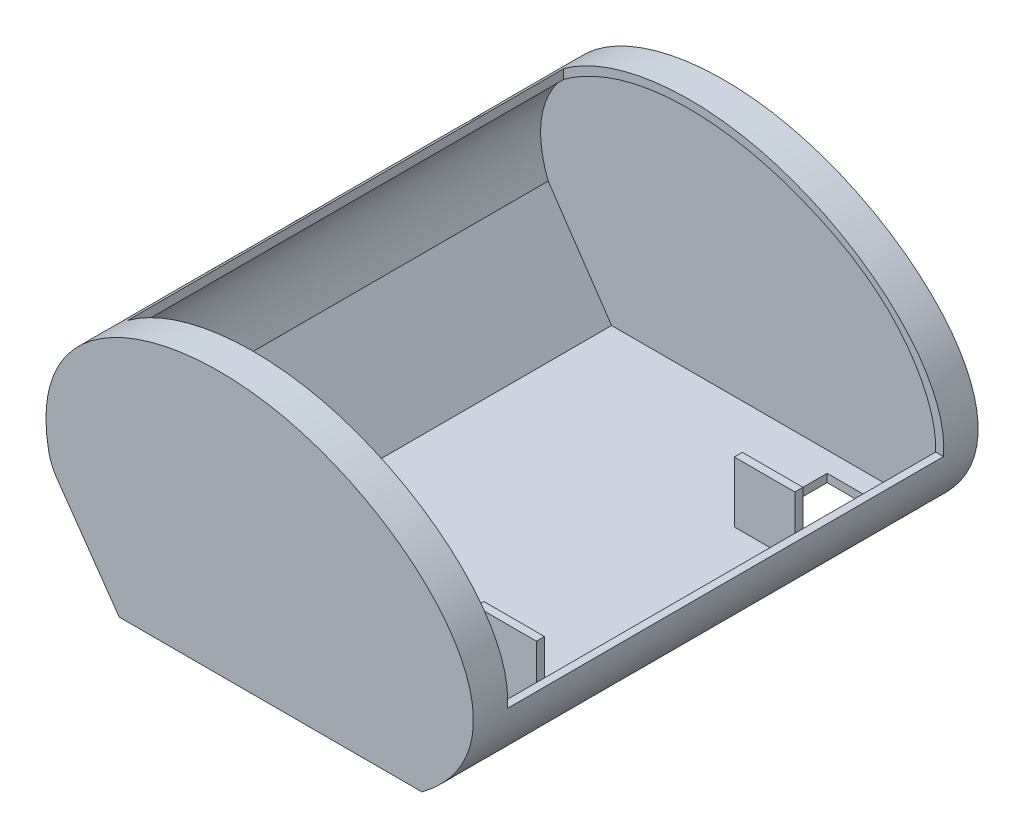
SolidWorks part; units mm, degrees
ref_plane "Front Plane" through (0, 0, 0) normal (0, 0, 1) x (1, 0, 0)
ref_plane "Top Plane" through (0, 0, 0) normal (0, 1, 0) x (1, 0, 0)
ref_plane "Right Plane" through (0, 0, 0) normal (1, 0, 0) x (0, 0, -1)
sketch "Sketch1" plane through (0, 0, 0) normal (0, 0, 1) x (1, 0, 0)
  line L0 (-74.4669, 0) -> (75.5331, 0)
  line L1 (-108.0812, 48.036) -> (-74.4669, 0)
  spline S0 degree 3 poles (75.5331, 0) (138.0634, 47.2005) (16.47, 172.0078) (-124.9496, 111.3016) (-108.0812, 48.036) knots 0 0 0 0 0.526875 1 1 1 1
  point P4 (-32.4145, 130)
  dimension "D1" = 150
  dimension "D2" = 130
extrude "Boss-Extrude1" add sketch "Sketch1" along normal blind 250
sketch "Sketch2" plane through (0, 0, 250) normal (0, 0, 1) x (1, 0, 0)
  line L0 (-105.0026, 50.2782) -> (-73.6035, 4)
  line L1 (-73.6035, 4) -> (73.1634, 4)
  line L2 (-74.4669, 0) -> (75.5331, 0) construction
  line L3 (-108.0812, 48.036) -> (-74.4669, 0) construction
  line L4 (73.1634, 4) -> (80.7933, 10.7284)
  spline S1 degree 3 poles (80.7933, 10.7284) (92.6518, 19.5638) (103.0098, 45.2056) (79.954, 88.9181) (40.6079, 112.9561) (-11.2048, 129.1427) (-79.4317, 124.6676) (-117.3447, 82.3238) (-105.0026, 50.2782) knots 0.016279 0.016279 0.016279 0.016279 0.126753 0.268313 0.414747 0.542883 0.761533 1 1 1 1
  spline S2 degree 3 poles (75.5331, 0) (138.0634, 47.2005) (16.47, 172.0078) (-124.9496, 111.3016) (-108.0812, 48.036) knots 0 0 0 0 0.526875 1 1 1 1 construction
  point P14 (40.9507, 114.8274)
  point P15 (100.9403, 42.4125)
  point P16 (-27.9262, 130.1717)
  point P17 (-96.6085, 104.0044)
  point P18 (-110.7265, 67.1672)
  point P19 (-108.4645, 63.8682)
  point P20 (-106.6025, 82.7288)
  point P21 (-109.6025, 78.5997)
  point P24 (-89.3031, 27.1391)
  dimension "D5" = 4
  dimension "D1" = 4
  dimension "D2" = 4
  dimension "D3" = 4
  dimension "D4" = 6
  dimension "D6" = 3
  dimension "D7" = 3.4043
extrude "Cut-Extrude1" cut sketch "Sketch2" against normal blind 236 from offset 7 offset against normal yes
sketch "Sketch3" plane through (0, 0, 0) normal (0, 1, 0) x (1, 0, 0)
  line L0 (-87.293, -17) -> (-87.293, -233)
  line L1 (-87.293, -233) -> (100.952, -233)
  line L2 (100.952, -250) -> (100.952, 0) construction
  line L3 (100.952, -233) -> (100.952, -17)
  line L4 (100.952, -17) -> (-87.293, -17)
  line L5 (100.952, 0) -> (-110.7265, 0) construction
  line L6 (-110.7265, -250) -> (100.952, -250) construction
  dimension "D1" = 17
  dimension "D2" = 17
extrude "Cut-Extrude2" cut sketch "Sketch3" along normal blind 236 from offset 40
fillet "Fillet1" radius 25 1 edges at (-108.0812, 48.036, 125)
sketch "Sketch6" plane through (0, 4, 0) normal (0, 1, 0) x (1, 0, 0)
  line L0 (73.1634, -187) -> (43.1634, -187)
  line L1 (73.1634, -7) -> (73.1634, -243) construction
  line L2 (43.1634, -187) -> (43.1634, -191)
  line L3 (43.1634, -191) -> (73.1634, -191)
  line L4 (73.1634, -191) -> (73.1634, -187)
  line L5 (100.952, -233) -> (-87.293, -233) construction
  dimension "D1" = 4
  dimension "D2" = 30
  dimension "D3" = 42
extrude "Boss-Extrude2" add sketch "Sketch6" along normal blind 30
sketch "Sketch7" plane through (0, 4, 0) normal (0, 1, 0) x (1, 0, 0)
  line L0 (73.1634, -191) -> (73.1634, -233)
  line L1 (100.952, -233) -> (-87.293, -233) construction
  line L2 (73.1634, -191) -> (73.1634, -243) construction
  line L3 (73.1634, -233) -> (43.1634, -233)
  line L4 (43.1634, -233) -> (43.1634, -191)
  line L5 (43.1634, -191) -> (73.1634, -191)
extrude "Cut-Extrude3" cut sketch "Sketch7" against normal through all both and the other way through all
sketch "Sketch8" plane through (0, 4, 0) normal (0, 1, 0) x (1, 0, 0)
  line L0 (73.1634, -59) -> (43.1634, -59)
  line L1 (73.1634, -7) -> (73.1634, -187) construction
  line L2 (43.1634, -59) -> (43.1634, -63)
  line L3 (43.1634, -63) -> (73.1634, -63)
  line L4 (73.1634, -63) -> (73.1634, -59)
  line L7 (-87.293, -17) -> (100.952, -17) construction
  dimension "D1" = 4
  dimension "D2" = 30
  dimension "D3" = 42
extrude "Boss-Extrude3" add sketch "Sketch8" along normal blind 30
sketch "Sketch9" plane through (0, 4, 0) normal (0, 1, 0) x (1, 0, 0)
  line L0 (43.1634, -59) -> (43.1634, -17)
  line L1 (-87.293, -17) -> (100.952, -17) construction
  line L2 (43.1634, -17) -> (73.1634, -17)
  line L3 (73.1634, -7) -> (73.1634, -59) construction
  line L4 (73.1634, -17) -> (73.1634, -59)
  line L5 (73.1634, -59) -> (43.1634, -59)
extrude "Cut-Extrude4" cut sketch "Sketch9" against normal through all both and the other way through all
